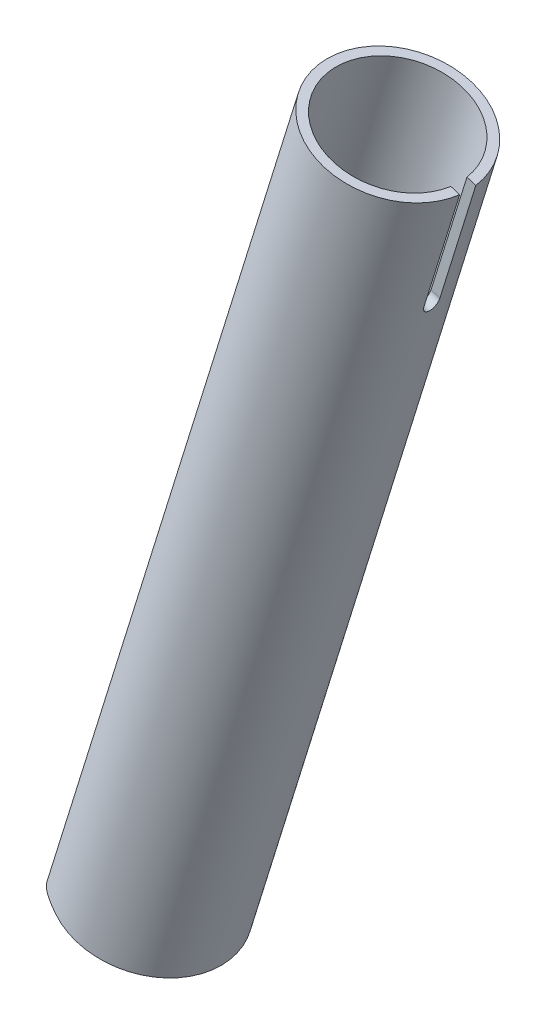
SolidWorks part; units mm, degrees
ref_plane "Plan de face" through (0, 0, 0) normal (0, 0, 1) x (1, 0, 0)
ref_plane "Plan de dessus" through (0, 0, 0) normal (0, 1, 0) x (1, 0, 0)
ref_plane "Plan de droite" through (0, 0, 0) normal (1, 0, 0) x (0, 0, -1)
sketch "Esquisse1" plane through (0, 0, 0) normal (0, 0, 1) x (1, 0, 0)
  line L0 (0, 0) -> (-619.8563, 51.5961) construction
  line L1 (0, 0) -> (-389.1874, 545.3743) construction
  line L2 (0, 0) -> (457.0972, 51.5961) construction
  line L3 (0, 0) -> (163.4516, 525.8703) construction
  line L4 (132.0822, 424.9462) -> (457.0972, 51.5961) construction
  line L5 (-489.2424, 277.5909) -> (-356.2649, 633.487) construction
  line L6 (-379.7372, 570.6665) -> (-22.8665, 389.9919) construction
  line L7 (-22.8665, 389.9919) -> (129.7077, 417.3067) construction
  dimension "D1" = 622
  dimension "D2" = 670
  dimension "D3" = 545
  dimension "D4" = 460
  dimension "D5" = 445
  dimension "D6" = 495
  dimension "D7" = 535
  dimension "D8" = 27
  dimension "D9" = 8
  dimension "D10" = 155
  dimension "D11" = 400
  dimension "D12" = 56
ref_plane "Plan6" through (0, 0, 0) normal (0.2968, 0.9549, 0) x (-0.9549, 0.2968, 0)
ref_plane "Plan7" through (148.407, 477.4677, 0) normal (0.2968, 0.9549, 0) x (-0.9549, 0.2968, 0)
ref_plane "Plan8" through (85.1856, 274.0664, 0) normal (0.2968, 0.9549, 0) x (-0.9549, 0.2968, 0)
sketch "Esquisse2" plane through (148.407, 477.4677, 0) normal (0.2968, 0.9549, 0) x (-0.9549, 0.2968, 0)
  circle A0 centre (0, 0) radius 16
  circle A1 centre (0, 0) radius 14
  dimension "D1" = 32
  dimension "D2" = 28
extrude "Extrusion5" add sketch "Esquisse2" against normal up to surface (213 mm away) up to plane "Plan8"
sketch "Esquisse12" plane through (0, 0, 0) normal (0, 0, 1) x (1, 0, 0)
  line L0 (67.6805, 271.6534) -> (76.585, 300.3015)
  line L1 (89.1025, 306.8827) -> (117.7505, 297.9783)
  line L2 (134.2036, 266.6846) -> (125.2991, 238.0365)
  line L3 (112.7816, 231.4553) -> (84.1336, 240.3597)
  line L4 (0, 0) -> (163.4516, 525.8703) construction
  line L9 (20.1137, 294.2922) -> (189.4834, 241.6485) construction
  line L10 (374.4143, 184.1681) -> (-204.0431, 363.9648) construction
  arc A0 (76.585, 300.3015) -> (89.1025, 306.8827) centre (86.1343, 297.3334) cw
  arc A1 (112.7816, 231.4553) -> (125.2991, 238.0365) centre (115.7498, 241.0046) ccw
  arc A2 (117.7505, 297.9783) -> (134.2036, 266.6846) centre (110.3302, 274.1049) cw
  arc A3 (67.6805, 271.6534) -> (84.1336, 240.3597) centre (91.5539, 264.2331) ccw
  point P8 (79.5531, 309.8509)
  point P11 (122.331, 228.4872)
  point P14 (141.6239, 290.5579)
  dimension "D3" = 10
  dimension "D4" = 25
  dimension "D1" = 65
  dimension "D2" = 65
  dimension "D7" = 16
extrude "Enlèv. mat.-Extru.1" cut sketch "Esquisse12" against normal through all and the other way through all
ref_plane "Plan9" through (0, 0, 0) normal (0.9549, -0.2968, 0) x (0, 0, -1)
sketch "Esquisse13" plane through (0, 0, 0) normal (0.9549, -0.2968, 0) x (0, 0, -1)
  line L0 (14, 500) -> (-14, 500) construction
  line L1 (-1.75, 500) -> (1.75, 500)
  line L2 (-1.75, 500) -> (-1.75, 473.75)
  line L3 (0, 0) -> (0, 550.6869) construction
  line L4 (1.75, 500) -> (1.75, 473.75)
  line L5 (16, 500) -> (-16, 500) construction
  arc A0 (1.75, 473.75) -> (-1.75, 473.75) centre (0, 473.75) cw
  dimension "D1" = 3.5
  dimension "D2" = 28
extrude "Enlèv. mat.-Extru.2" cut sketch "Esquisse13" along normal through all
